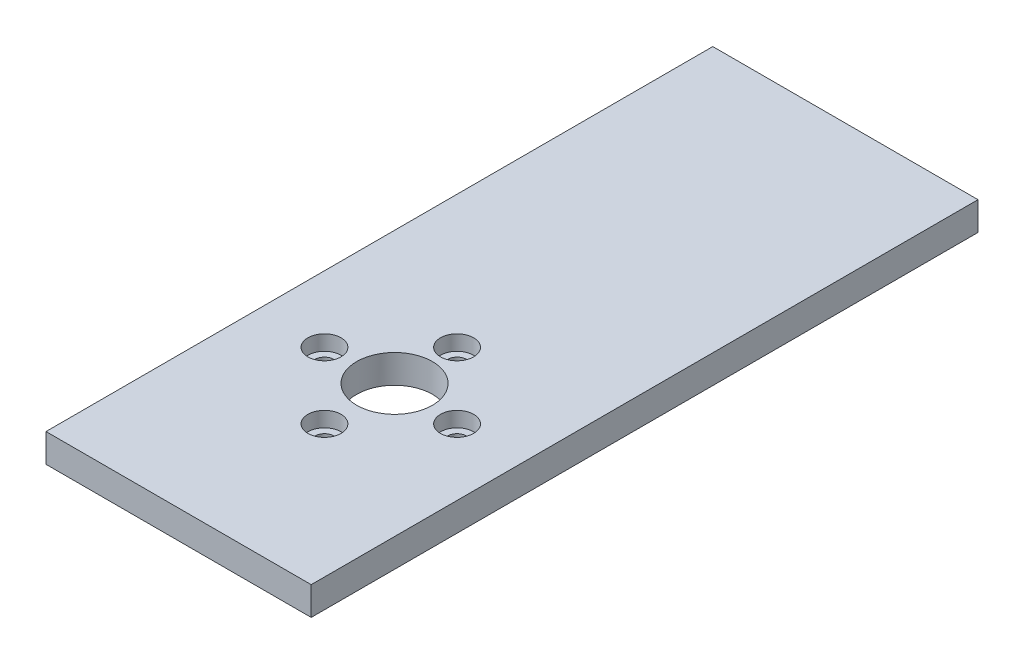
SolidWorks part; units mm, degrees
material "Custom Plastic"
ref_plane "Front Plane" through (0, 0, 0) normal (0, 0, 1) x (1, 0, 0)
ref_plane "Top Plane" through (0, 0, 0) normal (0, 1, 0) x (1, 0, 0)
ref_plane "Right Plane" through (0, 0, 0) normal (1, 0, 0) x (0, 0, -1)
sketch "Sketch1" plane through (0, 0, 0) normal (0, 1, 0) x (1, 0, 0)
  line L1 (-14, -35.2) -> (14, -35.2)
  line L2 (-14, -35.2) -> (-14, 35.2)
  line L3 (-14, 35.2) -> (14, 35.2)
  line L4 (14, -35.2) -> (14, 35.2)
  line L5 (-14, -35.2) -> (14, 35.2) construction
  line L6 (-14, 35.2) -> (14, -35.2) construction
  point P0 (0, 0)
  dimension "D1" = 70.4
  dimension "D2" = 28
extrude "Boss-Extrude1" add sketch "Sketch1" along normal blind 3
sketch "Sketch4" plane through (0, 3, 0) normal (0, 1, 0) x (1, 0, 0)
  line L0 (0, -2.5883) -> (0, -23.7562) construction
  line L1 (14, -35.2) -> (14, 35.2) construction
  circle A0 centre (7, -12.8) radius 1
  circle A1 centre (0, -19.8) radius 1
  circle A2 centre (-7, -12.8) radius 1
  circle A4 centre (0, -5.8) radius 1
  circle A9 centre (0, -12.8) radius 7 construction
  point P18 (0, -12.8)
  dimension "D1" = 2
  dimension "D2" = 14
  dimension "D4" = 14
  dimension "D3" = 4
extrude "Cut-Extrude2" cut sketch "Sketch4" against normal blind 10
sketch "Sketch5" plane through (0, 3, 0) normal (0, 1, 0) x (1, 0, 0)
  line L2 (-14, -35.2) -> (14, -35.2) construction
  line L3 (14, -35.2) -> (14, 35.2) construction
  circle A0 centre (0, -12.4) radius 4
  dimension "D1" = 8
  dimension "D2" = 22.8
  dimension "D3" = 14
extrude "Cut-Extrude3" cut sketch "Sketch5" against normal blind 10
sketch "Sketch10" plane through (0, 3, 0) normal (0, 1, 0) x (1, 0, 0)
  circle A0 centre (0, -19.8) radius 1.75
  circle A1 centre (-7, -12.8) radius 1.75
  circle A2 centre (0, -5.8) radius 1.75
  circle A3 centre (7, -12.8) radius 1.75
  dimension "D1" = 3.5
  dimension "D2" = 3.5
  dimension "D3" = 3.5
  dimension "D4" = 3.5
extrude "Cut-Extrude9" cut sketch "Sketch10" against normal blind 1.6
